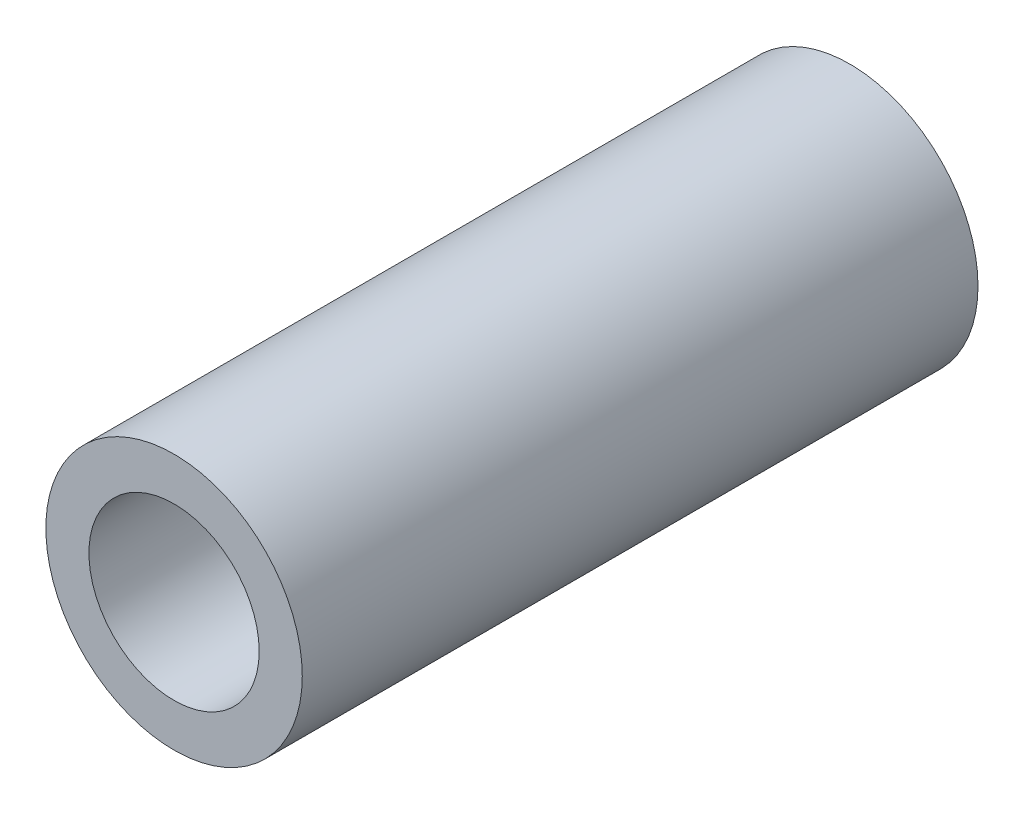
SolidWorks part; units mm, degrees
ref_plane "Front Plane" through (0, 0, 0) normal (0, 0, 1) x (1, 0, 0)
ref_plane "Top Plane" through (0, 0, 0) normal (0, 1, 0) x (1, 0, 0)
ref_plane "Right Plane" through (0, 0, 0) normal (1, 0, 0) x (0, 0, -1)
sketch "Sketch3" plane through (0, 0, 0) normal (0, 0, 1) x (1, 0, 0)
  circle A0 centre (0, 0) radius 2.3813
  circle A1 centre (0, 0) radius 2.3813 construction
  circle A2 centre (0, 0) radius 1.5813
  dimension "D1" = 0.8
sketch "Sketch4" plane through (0, 0, 0) normal (0, 1, 0) x (1, 0, 0)
  line L1 (-2.3813, 0) -> (2.3813, 0)
  line L2 (-2.3813, 0) -> (-2.3812, -12.55)
  line L3 (-2.3812, -12.55) -> (2.3813, -12.55)
  line L4 (2.3813, 0) -> (2.3813, -12.55)
  line L7 (0, 0) -> (0, -12.55) construction
  line L8 (-2.25, -0.15) -> (-2.25, -12.7) construction
extrude "Boss-Extrude1" add sketch "Sketch3" along normal up to vertex (12.55 mm away) up to point (-2.3812, 0, 12.55)
